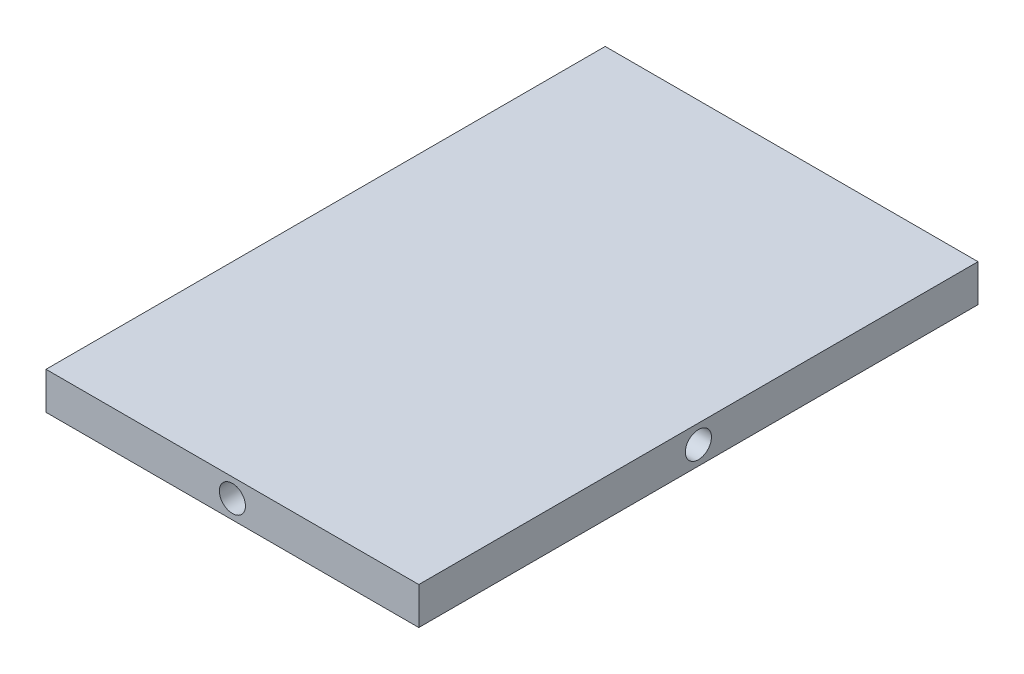
SolidWorks part; units mm, degrees
ref_plane "前视基准面" through (0, 0, 0) normal (0, 0, 1) x (1, 0, 0)
ref_plane "上视基准面" through (0, 0, 0) normal (0, 1, 0) x (1, 0, 0)
ref_plane "右视基准面" through (0, 0, 0) normal (1, 0, 0) x (0, 0, -1)
sketch "草图1" plane through (0, 0, 0) normal (0, 1, 0) x (1, 0, 0)
  line L1 (-50, -75) -> (50, -75)
  line L2 (-50, -75) -> (-50, 75)
  line L3 (-50, 75) -> (50, 75)
  line L4 (50, -75) -> (50, 75)
  line L5 (-50, -75) -> (50, 75) construction
  line L6 (-50, 75) -> (50, -75) construction
  point P0 (0, 0)
extrude "凸台-拉伸1" add sketch "草图1" along normal blind 10
sketch "草图2" plane through (0, 0, 75) normal (0, 0, 1) x (1, 0, 0)
  line L0 (-50, 10) -> (50, 0)
  line L1 (-50, 0) -> (50, 0) construction
  line L2 (50, 10) -> (50, 0) construction
  line L3 (50, 0) -> (50, 10)
  line L4 (50, 10) -> (-50, 0)
  circle A0 centre (0, 5) radius 3.5
extrude "切除-拉伸1" cut sketch "草图2" against normal blind 10 contours A0
sketch "草图3" plane through (50, 0, 0) normal (1, 0, 0) x (0, 0, -1)
  line L0 (-75, 10) -> (75, 0)
  line L1 (75, 0) -> (75, 10)
  line L2 (75, 10) -> (-75, 0)
  circle A0 centre (0, 5) radius 3.5
extrude "切除-拉伸2" cut sketch "草图3" against normal blind 10 contours A0
sketch "草图4" plane through (0, 0, -75) normal (0, 0, -1) x (-1, 0, 0)
  line L0 (-50, 10) -> (50, 0)
  line L1 (50, 0) -> (50, 10)
  line L2 (50, 10) -> (-50, 0)
  circle A0 centre (0, 5) radius 3.5
extrude "切除-拉伸3" cut sketch "草图4" against normal blind 10 contours L2 A0 L0 | L2 A0 L0 | L0 A0 L2 | L0 A0 L2
sketch "草图5" plane through (-50, 0, 0) normal (-1, 0, 0) x (0, 0, 1)
  line L0 (-75, 10) -> (75, 0)
  line L1 (75, 0) -> (75, 10)
  line L2 (75, 10) -> (-75, 0)
  circle A0 centre (0, 5) radius 3.5
extrude "切除-拉伸4" cut sketch "草图5" against normal blind 10 contours A0
